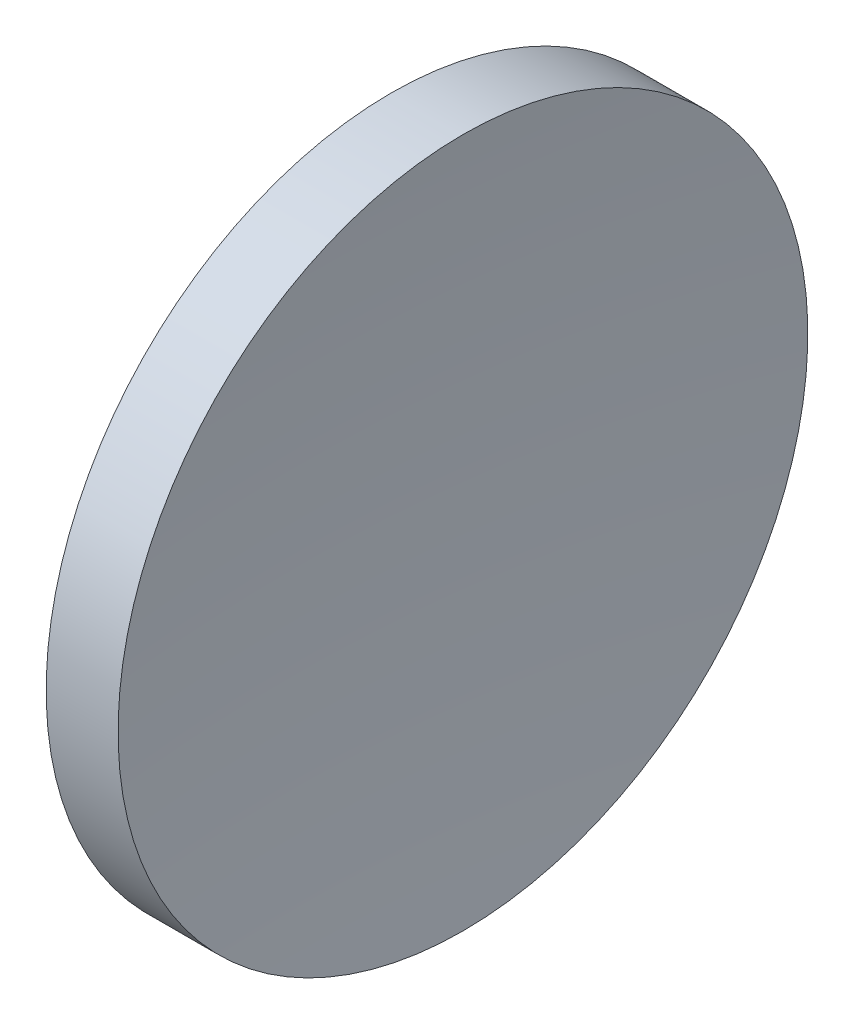
SolidWorks part; units mm, degrees
ref_plane "前视基准面" through (0, 0, 0) normal (0, 0, 1) x (1, 0, 0)
ref_plane "上视基准面" through (0, 0, 0) normal (0, 1, 0) x (1, 0, 0)
ref_plane "右视基准面" through (0, 0, 0) normal (1, 0, 0) x (0, 0, -1)
sketch "草图1" plane through (0, 0, 0) normal (0, 0, 1) x (1, 0, 0)
  line L0 (55.0074, 32.5787) -> (64.0943, 32.5787) construction
  line L1 (57.3582, 32.5787) -> (57.3582, 45.0787)
  line L2 (59.3582, 32.5787) -> (57.3582, 32.5787)
  line L3 (57.3582, 45.0787) -> (59.9646, 45.0787)
  arc A0 (59.9646, 45.0787) -> (59.3582, 32.5787) centre (188.4882, 32.5787) ccw
revolve "旋转1" add sketch "草图1" angle 360 about L0
